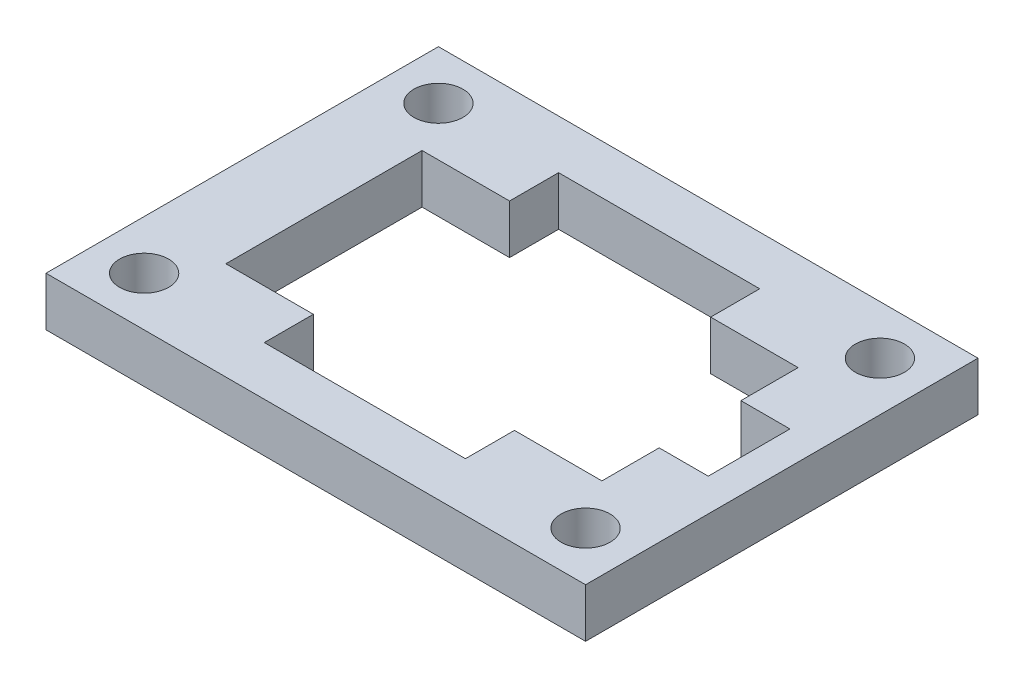
SolidWorks part; units mm, degrees
ref_plane "Front Plane" through (0, 0, 0) normal (0, 0, 1) x (1, 0, 0)
ref_plane "Top Plane" through (0, 0, 0) normal (0, 1, 0) x (1, 0, 0)
ref_plane "Right Plane" through (0, 0, 0) normal (1, 0, 0) x (0, 0, -1)
sketch "Sketch1" plane through (0, 0, 0) normal (0, 1, 0) x (1, 0, 0)
  line L1 (0, 0) -> (33, 0)
  line L2 (0, 0) -> (0, 24)
  line L3 (0, 24) -> (33, 24)
  line L4 (33, 0) -> (33, 24)
  dimension "D1" = 33
  dimension "D2" = 24
extrude "Boss-Extrude1" add sketch "Sketch1" along normal blind 3
sketch "Sketch2" plane through (0, 3, 0) normal (0, 1, 0) x (1, 0, 0)
  line L0 (16.5, 18) -> (16.5, 21) construction
  line L5 (5, 18) -> (28, 18)
  line L6 (5, 18) -> (5, 6)
  line L7 (5, 6) -> (28, 6)
  line L8 (28, 18) -> (28, 6)
  line L9 (10.5, 18) -> (22.5, 18)
  line L10 (10.5, 18) -> (10.5, 21)
  line L11 (10.5, 21) -> (22.5, 21)
  line L12 (22.5, 18) -> (22.5, 21)
  line L13 (10.5, 6) -> (22.5, 6)
  line L14 (10.5, 6) -> (10.5, 3)
  line L15 (10.5, 3) -> (22.5, 3)
  line L16 (22.5, 6) -> (22.5, 3)
  line L17 (28, 14.5) -> (29.5, 14.5)
  line L18 (28, 14.5) -> (28, 9.5)
  line L19 (28, 9.5) -> (29.5, 9.5)
  line L20 (29.5, 14.5) -> (29.5, 9.5)
  line L21 (0, 24) -> (0, 0) construction
  line L22 (28, 12) -> (29.5, 12) construction
  line L23 (33, 24) -> (0, 24) construction
  line L24 (33, 0) -> (33, 24) construction
  line L25 (0, 0) -> (33, 0) construction
  circle A0 centre (3, 21) radius 1.5
  circle A1 centre (30, 21) radius 1.5
  circle A2 centre (30, 3) radius 1.5
  circle A3 centre (3, 3) radius 1.5
  point P36 (0, 0)
  point P38 (33.4, 19.6972)
  dimension "D9" = 3
  dimension "D1" = 23
  dimension "D2" = 12
  dimension "D3" = 5
  dimension "D4" = 3
  dimension "D5" = 5
  dimension "D6" = 1.5
  dimension "D7" = 12
  dimension "D8" = 3
  dimension "D10" = 3
  dimension "D11" = 3
  dimension "D12" = 3
  dimension "D13" = 3
extrude "Cut-Extrude1" cut sketch "Sketch2" against normal through all contours L8 L5 L6 L7 | L20 L17 L8 L19 | A1 | L16 L7 L14 L15 | L5 L12 L11 L10 | A2 | A3 | A0
sketch "Sketch3" plane through (0, 3, 0) normal (0, 1, 0) x (1, 0, 0)
  line L0 (10.5, 3) -> (22.5, 3) construction
  line L1 (10.5, 18) -> (10.35, 18)
  line L2 (10.5, 18) -> (10.5, 21)
  line L3 (10.5, 21) -> (10.35, 21)
  line L4 (10.35, 18) -> (10.35, 21)
  line L5 (22.5, 18) -> (22.65, 18)
  line L6 (22.5, 18) -> (22.5, 21)
  line L7 (22.5, 21) -> (22.65, 21)
  line L8 (22.65, 18) -> (22.65, 21)
  line L9 (22.5, 6) -> (22.65, 6)
  line L10 (22.5, 6) -> (22.5, 3)
  line L11 (22.5, 3) -> (22.65, 3)
  line L12 (22.65, 6) -> (22.65, 3)
  line L13 (10.5, 6) -> (10.35, 6)
  line L14 (10.5, 6) -> (10.5, 3)
  line L15 (10.5, 3) -> (10.35, 3)
  line L16 (10.35, 6) -> (10.35, 3)
  line L17 (10.5, 21) -> (22.5, 21) construction
  line L18 (28, 9.5) -> (29.5, 9.5) construction
  line L19 (29.5, 14.5) -> (31, 14.5)
  line L20 (29.5, 14.5) -> (29.5, 9.5)
  line L21 (29.5, 9.5) -> (31, 9.5)
  line L22 (31, 14.5) -> (31, 9.5)
  dimension "D1" = 0.15
  dimension "D2" = 1.5
extrude "Cut-Extrude2" cut sketch "Sketch3" against normal through all
